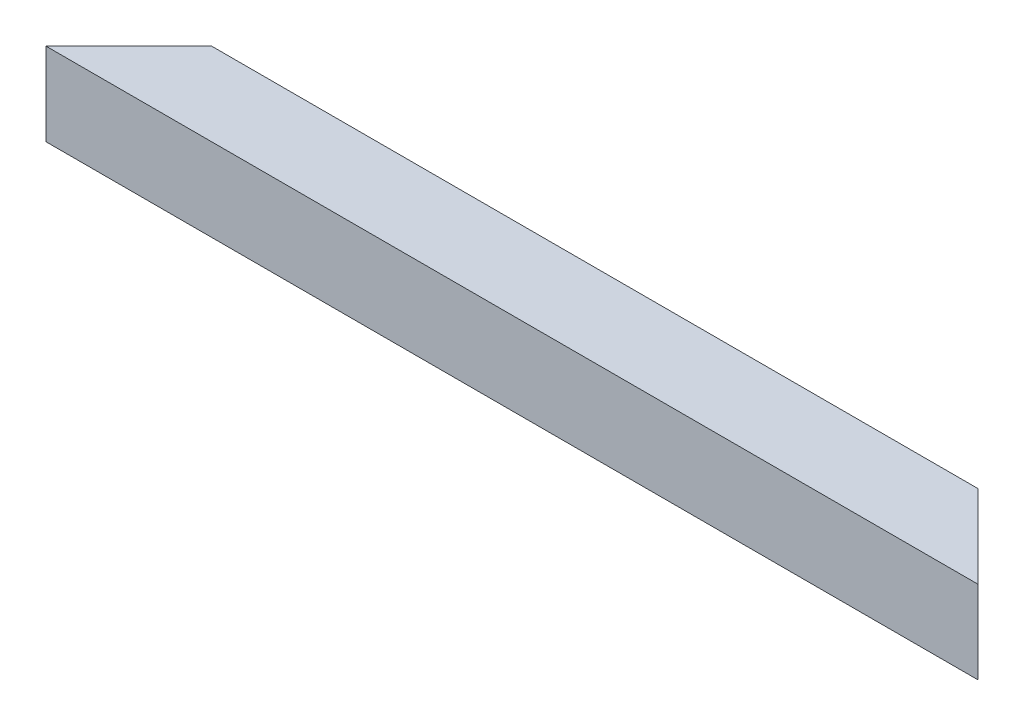
SolidWorks part; units mm, degrees
ref_plane "Alzado" through (0, 0, 0) normal (0, 0, 1) x (1, 0, 0)
ref_plane "Planta" through (0, 0, 0) normal (0, 1, 0) x (1, 0, 0)
ref_plane "Vista lateral" through (0, 0, 0) normal (1, 0, 0) x (0, 0, -1)
sketch "Sketch1" plane through (0, 0, 0) normal (0, 1, 0) x (1, 0, 0)
  line L0 (0, 0) -> (285.8, 0)
  line L1 (285.8, 0) -> (285.8, 25.4)
  line L2 (285.8, 25.4) -> (0, 25.4)
  line L3 (0, 25.4) -> (0, 0)
  dimension "D1" = 285.8
  dimension "D2" = 25.4
extrude "Boss-Extrude1" add sketch "Sketch1" along normal blind 25.4
sketch "Sketch2" plane through (285.8, 0, 0) normal (1, 0, 0) x (0, 0, -1)
  line L0 (1.2, 24.2) -> (24.2, 24.2)
  line L1 (24.2, 24.2) -> (24.2, 1.2)
  line L2 (1.2, 24.2) -> (1.2, 1.2)
  line L3 (1.2, 1.2) -> (24.2, 1.2)
  line L4 (0, 25.4) -> (0, 0) construction
  line L5 (0, 25.4) -> (25.4, 25.4) construction
  line L6 (25.4, 25.4) -> (25.4, 0) construction
  line L7 (0, 0) -> (25.4, 0) construction
  dimension "D1" = 1.2
  dimension "D2" = 1.2
  dimension "D3" = 1.2
  dimension "D4" = 1.2
extrude "Cut-Extrude1" cut sketch "Sketch2" against normal blind 450
sketch "Sketch3" plane through (0, 25.4, 0) normal (0, 1, 0) x (1, 0, 0)
  line L0 (0, 0) -> (25.4, 25.4)
  line L1 (285.8, 25.4) -> (0, 25.4) construction
  line L4 (0, 0) -> (0, 25.4)
  line L5 (0, 25.4) -> (25.4, 25.4)
  line L6 (285.8, 0) -> (260.4, 25.4)
  line L7 (260.4, 25.4) -> (285.8, 25.4)
  line L8 (285.8, 25.4) -> (285.8, 0)
  dimension "D1" = 25.4
  dimension "D2" = 25.4
extrude "Cut-Extrude2" cut sketch "Sketch3" against normal blind 25.4
